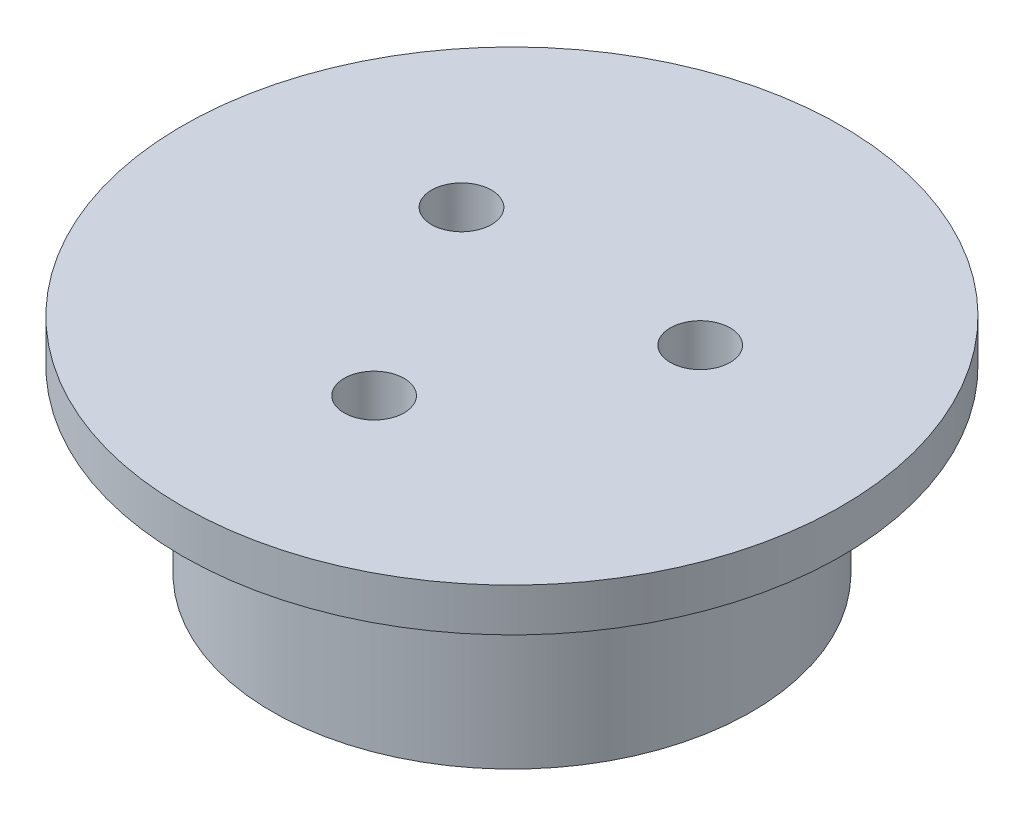
SolidWorks part; units mm, degrees
material "1060 Alloy"
ref_plane "Front Plane" through (0, 0, 0) normal (0, 0, 1) x (1, 0, 0)
ref_plane "Top Plane" through (0, 0, 0) normal (0, 1, 0) x (1, 0, 0)
ref_plane "Right Plane" through (0, 0, 0) normal (1, 0, 0) x (0, 0, -1)
sketch "Sketch1" plane through (0, 0, 0) normal (0, 1, 0) x (1, 0, 0)
  line L0 (0, 0) -> (0, 27.5) construction
  line L1 (0, 0) -> (9.9593, 5.75) construction
  line L2 (0, 0) -> (0, -11.5) construction
  line L3 (0, 0) -> (-9.9593, 5.75) construction
  circle A0 centre (0, 0) radius 27.5
  circle A1 centre (-9.9593, 5.75) radius 2.5
  circle A2 centre (9.9593, 5.75) radius 2.5
  circle A3 centre (0, -11.5) radius 2.5
  dimension "D3" = 5
  dimension "D4" = 55
  dimension "D1" = 120
  dimension "D2" = 120
  dimension "D5" = 11.5
extrude "Boss-Extrude1" add sketch "Sketch1" along normal blind 3.6
sketch "Sketch2" plane through (0, 0, 0) normal (0, -1, 0) x (1, 0, 0)
  circle A0 centre (0, 0) radius 20
  circle A1 centre (0, 11.5) radius 2.5
  circle A2 centre (9.9593, -5.75) radius 2.5
  circle A3 centre (-9.9593, -5.75) radius 2.5
  circle A4 centre (0, 11.5) radius 2.5 construction
  circle A5 centre (-9.9593, -5.75) radius 2.5 construction
  circle A6 centre (9.9593, -5.75) radius 2.5 construction
  dimension "D1" = 40
extrude "Boss-Extrude2" add sketch "Sketch2" along normal blind 15
sketch "Sketch3" plane through (0, -15, 0) normal (0, -1, 0) x (1, 0, 0)
  circle A0 centre (0, 0) radius 17.5
  dimension "D1" = 35
extrude "Cut-Extrude1" cut sketch "Sketch3" against normal blind 5
